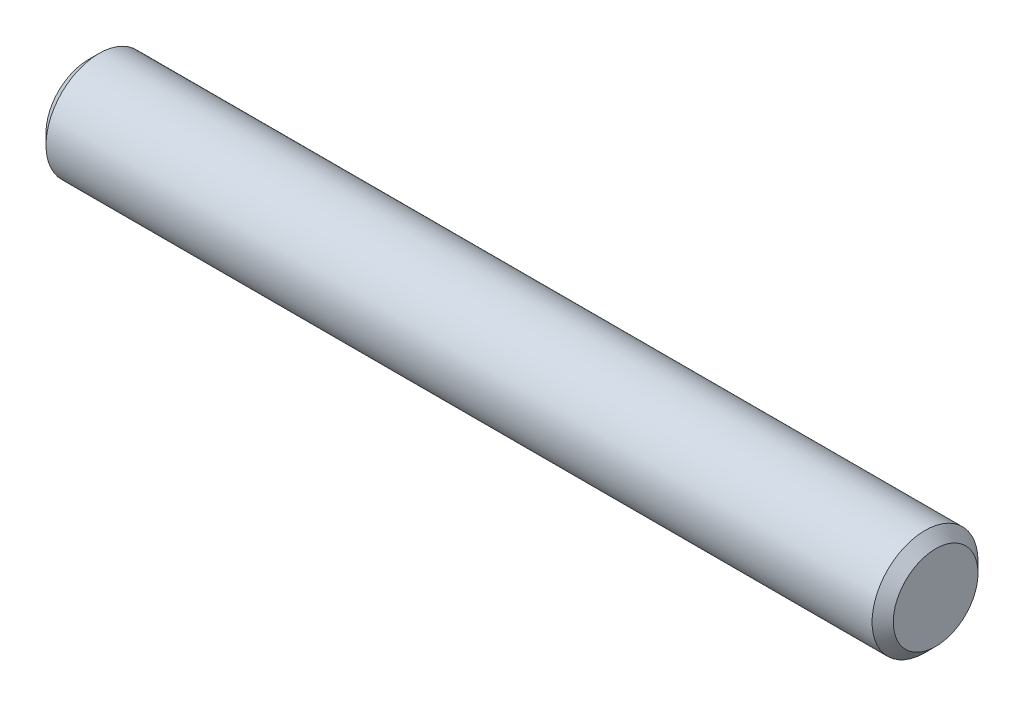
SolidWorks part; units mm, degrees
ref_plane "Front" through (0, 0, 0) normal (0, 0, 1) x (1, 0, 0)
ref_plane "Top" through (0, 0, 0) normal (0, 1, 0) x (1, 0, 0)
ref_plane "Right" through (0, 0, 0) normal (1, 0, 0) x (0, 0, -1)
sketch "Sketch1" plane through (0, 0, 0) normal (0, 0, 1) x (1, 0, 0)
  line L0 (-12.7, 0) -> (12.7, 0) construction
  line L1 (12.7, 1.5875) -> (12.7, -1.5875) construction
  line L2 (-12.7, 1.5875) -> (-12.7, -1.5875) construction
  dimension "Length" = 25.4
  dimension "Diameter" = 3.175
sketch "Sketch2" plane through (0, 0, 0) normal (1, 0, 0) x (0, 0, -1)
  circle A0 centre (0, 0) radius 1.5875
extrude "Extrude1" add sketch "Sketch2" against normal up to vertex (12.7 mm away) and the other way up to vertex (12.7 mm away) up to point (-12.7, 1.5875, 0) other way up to point (12.7, 1.5875, 0)
chamfer "Chamfer1" distance 0.3175 angle 45 2 edges at (12.7, 0, -1.5875) (-12.7, 0, -1.5875)
equation "\"D1@Chamfer1\" = \"Diameter@Sketch1\"*.1"
